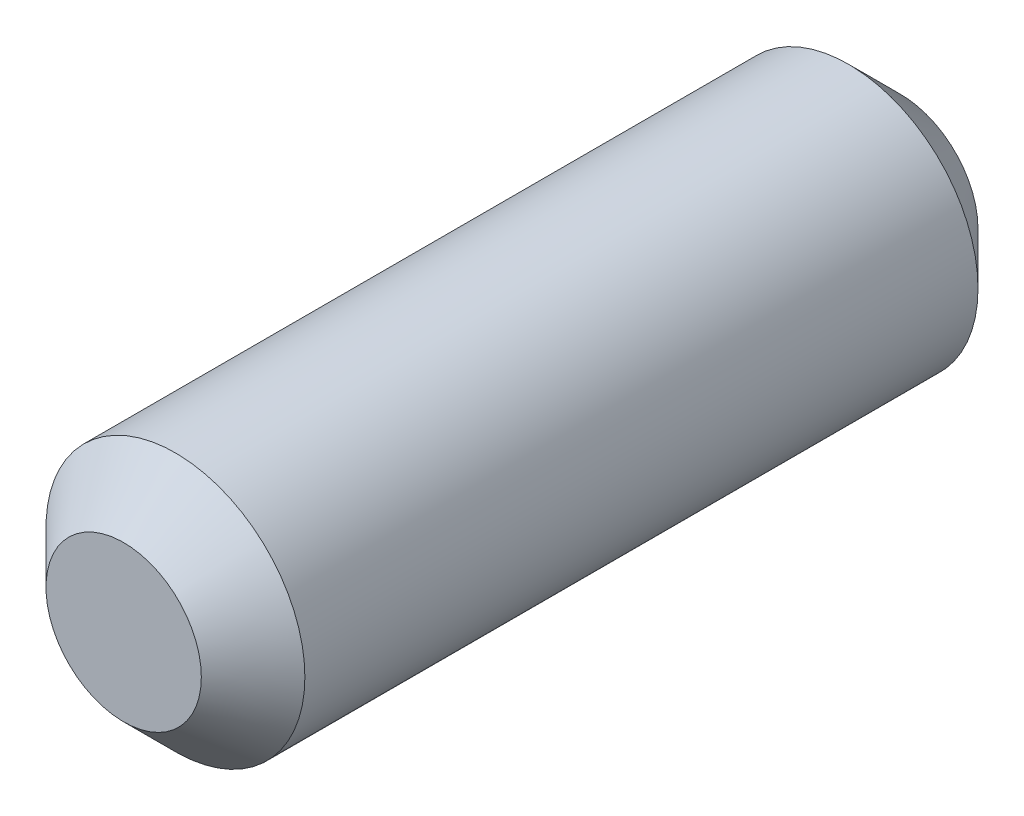
SolidWorks part; units mm, degrees
ref_plane "Front Plane" through (0, 0, 0) normal (0, 0, 1) x (1, 0, 0)
ref_plane "Top Plane" through (0, 0, 0) normal (0, 1, 0) x (1, 0, 0)
ref_plane "Right Plane" through (0, 0, 0) normal (1, 0, 0) x (0, 0, -1)
sketch "Sketch1" plane through (0, 0, 0) normal (0, 0, 1) x (1, 0, 0)
  circle A0 centre (0, 0) radius 6.35
  dimension "D1" = 12.7
extrude "Boss-Extrude1" add sketch "Sketch1" along normal blind 38.1
chamfer "Chamfer1" distance 2.54 angle 45 1 edges at (6.35, 0, 38.1)
chamfer "Chamfer2" distance 2.54 angle 45 1 edges at (6.35, 0, 0)
